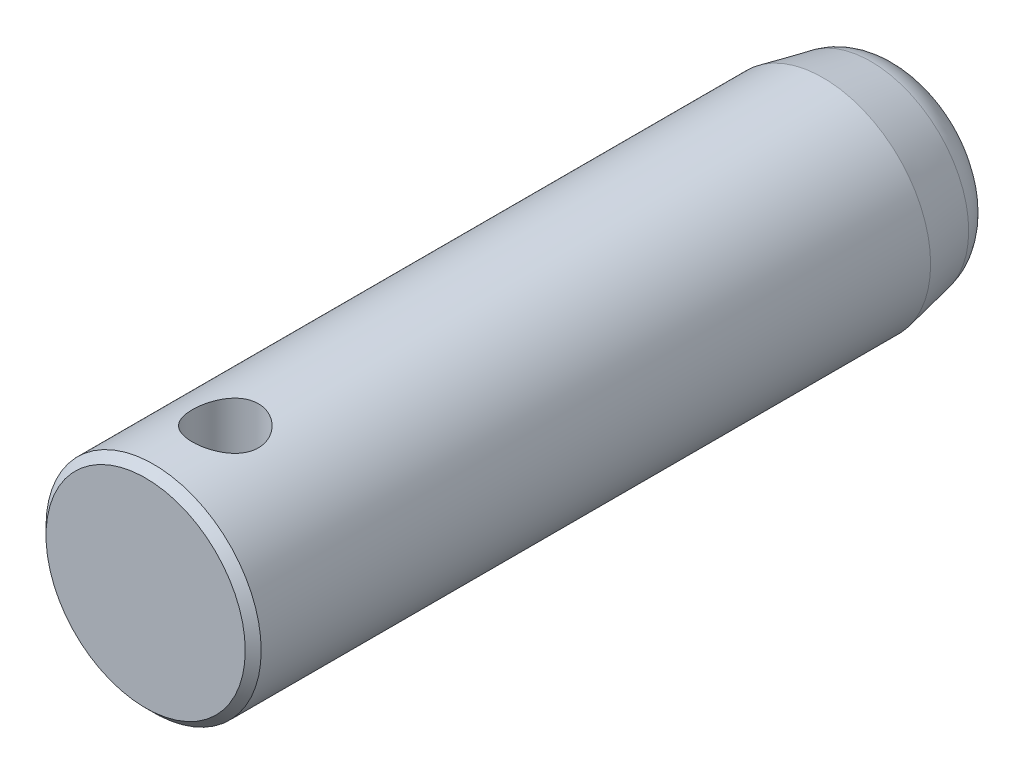
SolidWorks part; units mm, degrees
ref_plane "정면" through (0, 0, 0) normal (0, 0, 1) x (1, 0, 0)
ref_plane "평면" through (0, 0, 0) normal (0, 1, 0) x (1, 0, 0)
ref_plane "우측면" through (0, 0, 0) normal (1, 0, 0) x (0, 0, -1)
sketch "스케치1" plane through (0, 0, 0) normal (1, 0, 0) x (0, 0, -1)
  line L0 (0, 0) -> (95, 0) construction
  line L2 (1, 13.5) -> (85, 13.5)
  line L3 (0, 12.5) -> (0, 0)
  line L5 (0, 13.5) -> (95, 13.5) construction
  line L6 (0, 0) -> (95, 0)
  line L7 (85, 13.5) -> (90.9968, 12.2799)
  line L9 (95, 0) -> (95, 7.3803)
  line L10 (0, 12.5) -> (1, 13.5)
  arc A1 (95, 7.3803) -> (90.9968, 12.2799) centre (90, 7.3803) ccw
  dimension "D1" = 13.5
  dimension "D3" = 5
  dimension "D2" = 1
  dimension "D4" = 11.5
  dimension "D5" = 95
  dimension "D6" = 85
  dimension "D7" = 1
revolve "회전1" add sketch "스케치1" angle 360 about L6
ref_plane "평면1" through (0, 13.5, 0) normal (0, 1, 0) x (1, 0, 0)
sketch "스케치2" plane through (0, 13.5, 0) normal (0, 1, 0) x (1, 0, 0)
  line L0 (0, 0) -> (0, 10) construction
  line L1 (-12.5, 0) -> (12.5, 0) construction
  circle A0 centre (0, 10) radius 4.15
  dimension "D1" = 8.3
  dimension "D2" = 10
extrude "컷-돌출1" cut sketch "스케치2" against normal up to next
